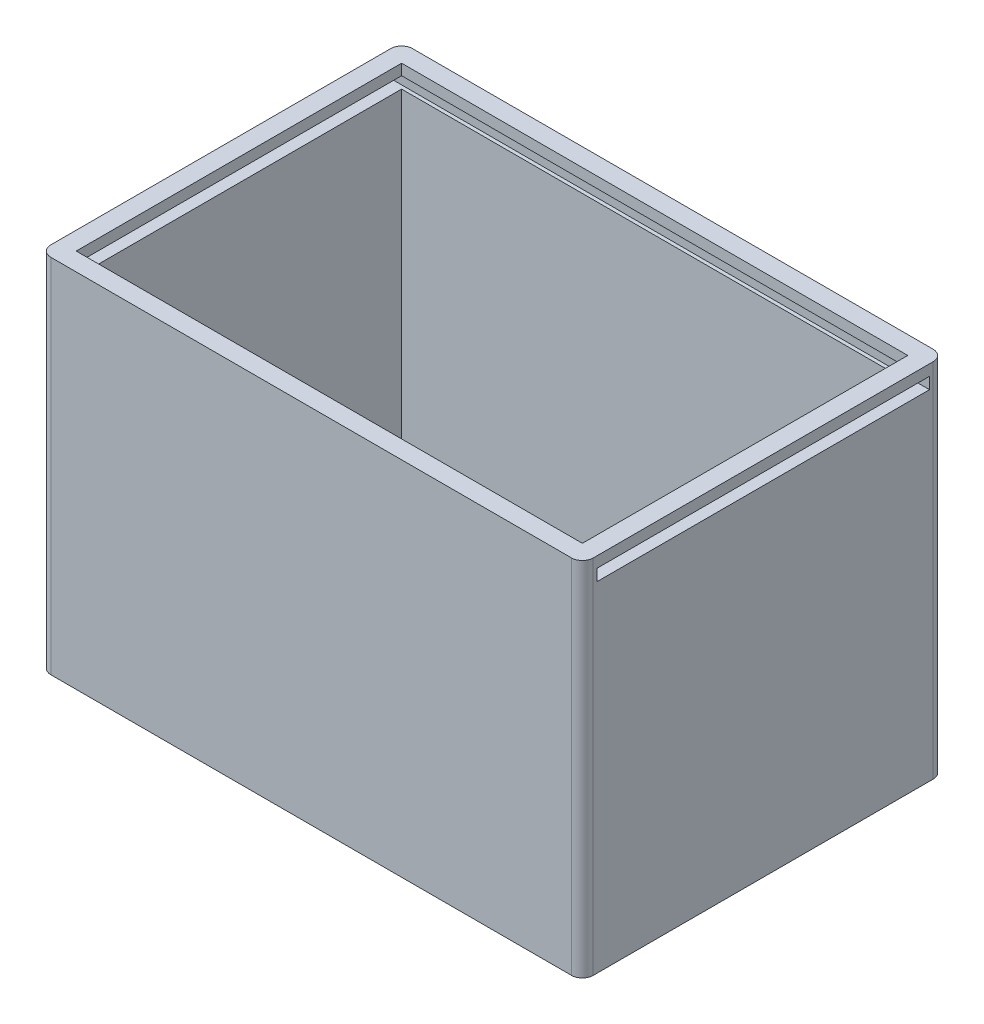
SolidWorks part; units mm, degrees
ref_plane "Front Plane" through (0, 0, 0) normal (0, 0, 1) x (1, 0, 0)
ref_plane "Top Plane" through (0, 0, 0) normal (0, 1, 0) x (1, 0, 0)
ref_plane "Right Plane" through (0, 0, 0) normal (1, 0, 0) x (0, 0, -1)
sketch "Sketch2" plane through (0, 0, 0) normal (0, 1, 0) x (1, 0, 0)
  line L1 (-72, 50) -> (72, 50)
  line L2 (-75, 47) -> (-75, -47)
  line L3 (-72, -50) -> (72, -50)
  line L4 (75, 47) -> (75, -47)
  line L5 (-75, 50) -> (75, -50) construction
  line L6 (-75, -50) -> (75, 50) construction
  arc A0 (75, 47) -> (72, 50) centre (72, 47) ccw
  arc A1 (72, -50) -> (75, -47) centre (72, -47) ccw
  arc A2 (-75, -47) -> (-72, -50) centre (-72, -47) ccw
  arc A3 (-72, 50) -> (-75, 47) centre (-72, 47) ccw
  point P0 (0, 0)
  dimension "D3" = 3
  dimension "D4" = 3
  dimension "D5" = 3
  dimension "D6" = 3
  dimension "D1" = 100
  dimension "D2" = 150
extrude "Boss-Extrude1" add sketch "Sketch2" along normal blind 100
ref_plane "Plane1" through (0, 110, 0) normal (0, 1, 0) x (1, 0, 0)
sketch "Sketch3" plane through (0, 110, 0) normal (0, 1, 0) x (1, 0, 0)
  line L0 (72, 50) -> (-72, 50) construction
  line L1 (-70, 45) -> (70, 45)
  line L2 (-70, 45) -> (-70, -45)
  line L3 (-70, -45) -> (70, -45)
  line L4 (70, 45) -> (70, -45)
  line L5 (-70, 45) -> (70, -45) construction
  line L6 (-70, -45) -> (70, 45) construction
  line L7 (75, -47) -> (75, 47) construction
  point P0 (0, 0)
  dimension "D1" = 5
  dimension "D2" = 5
extrude "Cut-Extrude1" cut sketch "Sketch3" against normal blind 105
ref_plane "Plane2" through (85, 0, 0) normal (1, 0, 0) x (0, 0, -1)
sketch "Sketch4" plane through (85, 0, 0) normal (1, 0, 0) x (0, 0, -1)
  line L0 (-47, 100) -> (47, 100) construction
  line L1 (-46, 97) -> (46, 97)
  line L2 (-46, 97) -> (-46, 93.8)
  line L3 (-46, 93.8) -> (46, 93.8)
  line L4 (46, 97) -> (46, 93.8)
  line L5 (50, 100) -> (50, 0) construction
  line L6 (-50, 100) -> (-50, 0) construction
  point P8 (-46, 95.4)
  dimension "D1" = 3.2
  dimension "D2" = 3
  dimension "D3" = 4
  dimension "D4" = 4
extrude "Cut-Extrude2" cut sketch "Sketch4" against normal blind 170
ref_plane "Plane3" through (0, 0, -60) normal (0, 0, -1) x (-1, 0, 0)
sketch "Sketch5" plane through (0, 0, -60) normal (0, 0, -1) x (-1, 0, 0)
  text T0 "<b>PHM66</b>" font "Century Gothic" height in points 35
extrude "Cut-Extrude3" cut sketch "Sketch5" against normal blind 12
